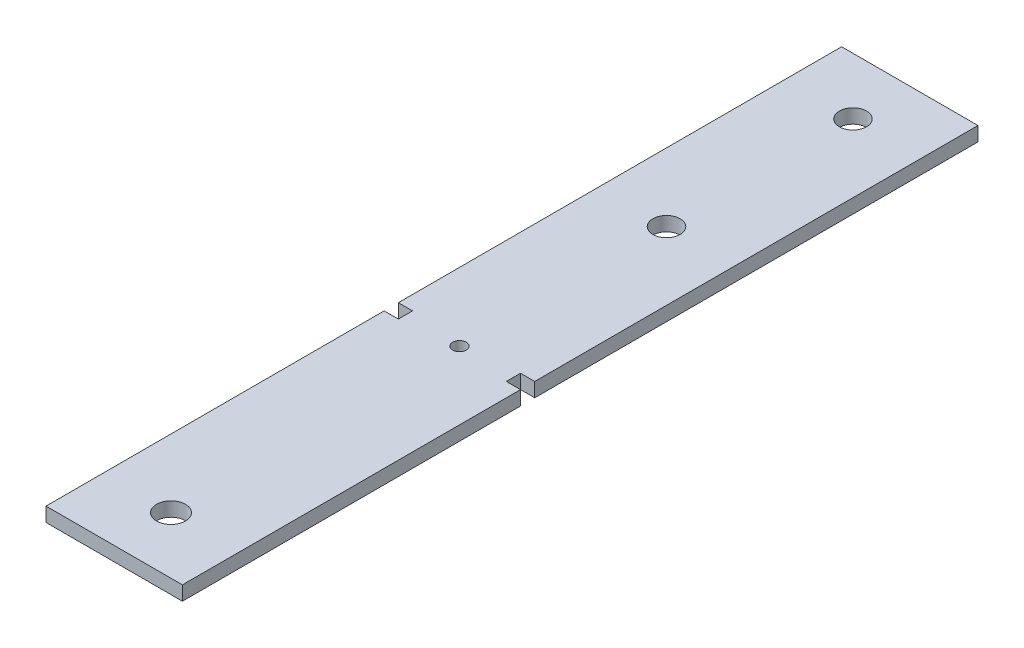
SolidWorks part; units mm, degrees
ref_plane "Front Plane" through (0, 0, 0) normal (0, 0, 1) x (1, 0, 0)
ref_plane "Top Plane" through (0, 0, 0) normal (0, 1, 0) x (1, 0, 0)
ref_plane "Right Plane" through (0, 0, 0) normal (1, 0, 0) x (0, 0, -1)
sketch "Sketch1" plane through (0, 0, 0) normal (0, 1, 0) x (1, 0, 0)
  line L0 (-17.2798, 88.9) -> (-17.2798, -10.16)
  line L1 (-17.2798, -88.9) -> (-47.7598, -88.9)
  line L2 (-17.2798, 88.9) -> (-47.7598, 88.9)
  line L3 (-47.7598, 88.9) -> (-47.7598, -10.16)
  line L4 (-47.7598, -10.16) -> (-44.5848, -10.16)
  line L5 (-44.5848, -10.16) -> (-44.5848, -13.335)
  line L6 (-44.5848, -13.335) -> (-47.7598, -13.335)
  line L7 (-17.2798, -13.335) -> (-20.4548, -13.335)
  line L8 (-20.4548, -13.335) -> (-20.4548, -10.16)
  line L9 (-20.4548, -10.16) -> (-17.2798, -10.16)
  line L10 (-47.7598, -13.335) -> (-47.7598, -88.9)
  line L11 (-17.2798, -13.335) -> (-17.2798, -88.9)
  circle A0 centre (-32.5198, -11.7475) radius 1.524
  circle A1 centre (-32.5198, 34.5293) radius 3.048
  circle A2 centre (-32.5198, 76.2) radius 3.048
  circle A3 centre (-32.5198, -76.2) radius 3.2385
  point P14 (-20.4548, -11.7475)
  dimension "D3" = 3.048
  dimension "D1" = 3.175
  dimension "D2" = 3.175
extrude "Boss-Extrude1" add sketch "Sketch1" along normal blind 3.175
